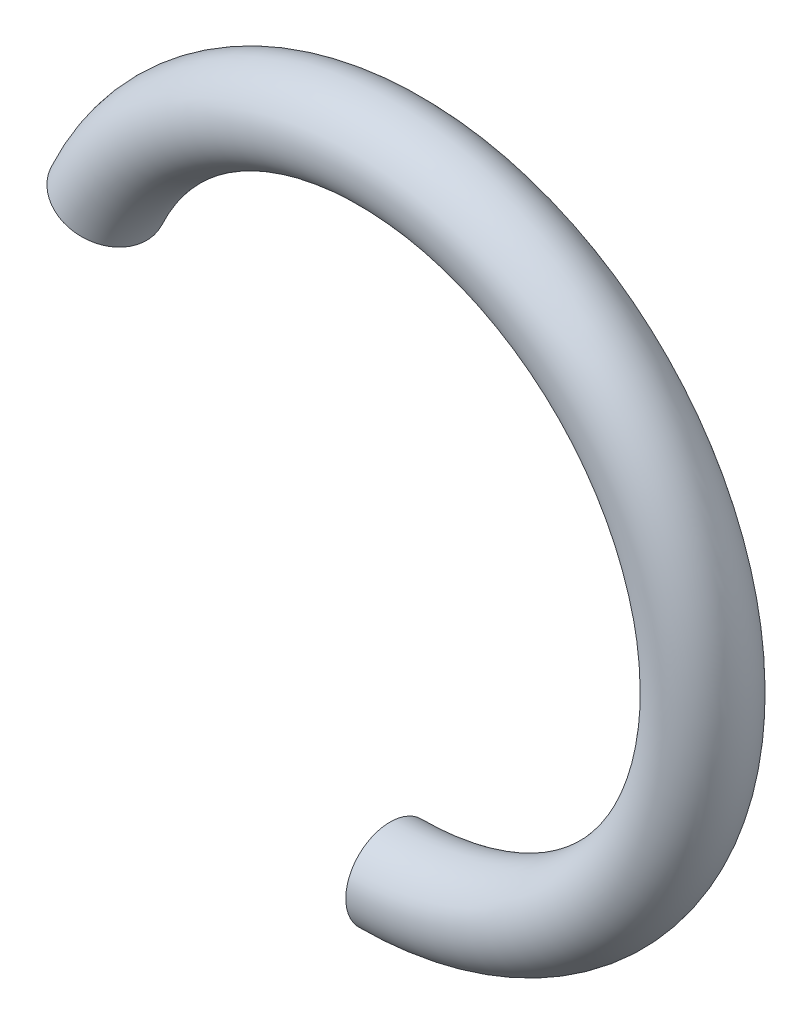
SolidWorks part; units mm, degrees
material "Cast Alloy Steel"
ref_plane "Front Plane" through (0, 0, 0) normal (0, 0, 1) x (1, 0, 0)
ref_plane "Top Plane" through (0, 0, 0) normal (0, 1, 0) x (1, 0, 0)
ref_plane "Right Plane" through (0, 0, 0) normal (1, 0, 0) x (0, 0, -1)
sketch "Sketch1" plane through (0, 0, 0) normal (0, 0, 1) x (1, 0, 0)
  line L2 (-4.169, 1.944) -> (0, 0) construction
  line L3 (0, 0) -> (0, -4.6) construction
  arc A0 (0, -4.6) -> (-4.169, 1.944) centre (0, 0) ccw
  dimension "D1" = 9.2
  dimension "D2" = 115
sketch "Sketch2" plane through (0, 0, 0) normal (1, 0, 0) x (0, 0, -1)
  line L0 (0, 0) -> (0, -4.6) construction
  line L1 (0, 0) -> (0, -4.6) construction
  circle A0 centre (0, -4.6) radius 0.65
  dimension "D1" = 1.3
  dimension "D2" = 4.6
sweep "Sweep1" add profiles "Sketch2" path "Sketch1"
